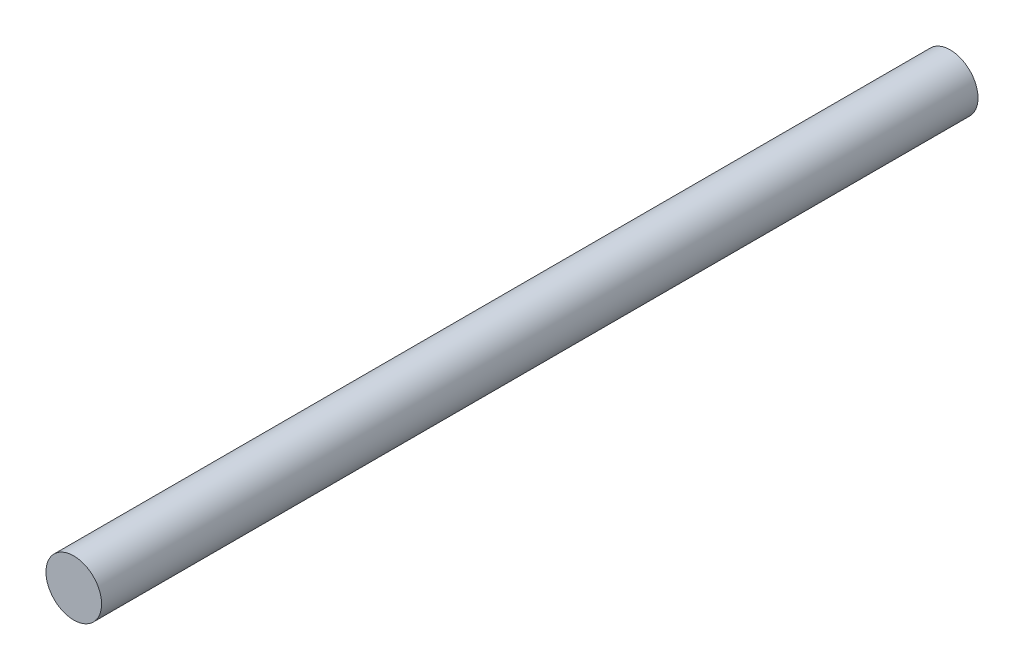
SolidWorks part; units mm, degrees
ref_plane "Přední rovina" through (0, 0, 0) normal (0, 0, 1) x (1, 0, 0)
ref_plane "Horní rovina" through (0, 0, 0) normal (0, 1, 0) x (1, 0, 0)
ref_plane "Pravá rovina" through (0, 0, 0) normal (1, 0, 0) x (0, 0, -1)
sketch "Skica1" plane through (0, 0, 0) normal (0, 0, 1) x (1, 0, 0)
  circle A0 centre (0, 0) radius 1.65
  dimension "D1" = 3.3
extrude "Přidat vysunutím1" add sketch "Skica1" along normal blind 52
